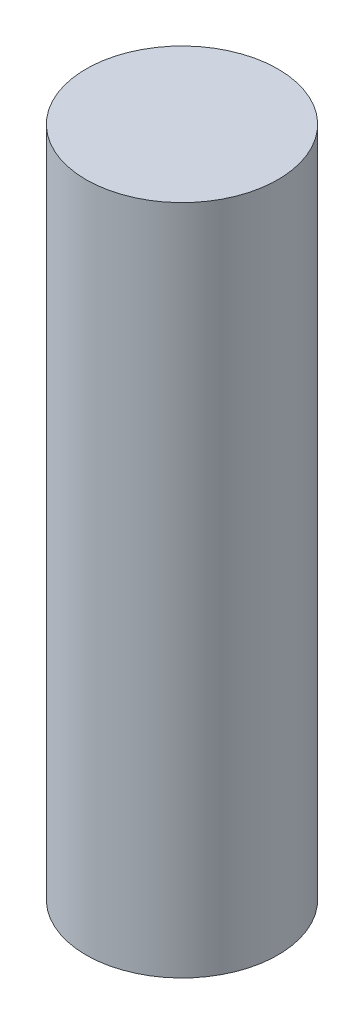
SolidWorks part; units mm, degrees
ref_plane "Alzado" through (0, 0, 0) normal (0, 0, 1) x (1, 0, 0)
ref_plane "Planta" through (0, 0, 0) normal (0, 1, 0) x (1, 0, 0)
ref_plane "Vista lateral" through (0, 0, 0) normal (1, 0, 0) x (0, 0, -1)
sketch "Croquis1" plane through (0, 0, 0) normal (0, 1, 0) x (1, 0, 0)
  circle A0 centre (0, 0) radius 2
  dimension "D1" = 4
extrude "Saliente-Extruir1" add sketch "Croquis1" along normal blind 14
